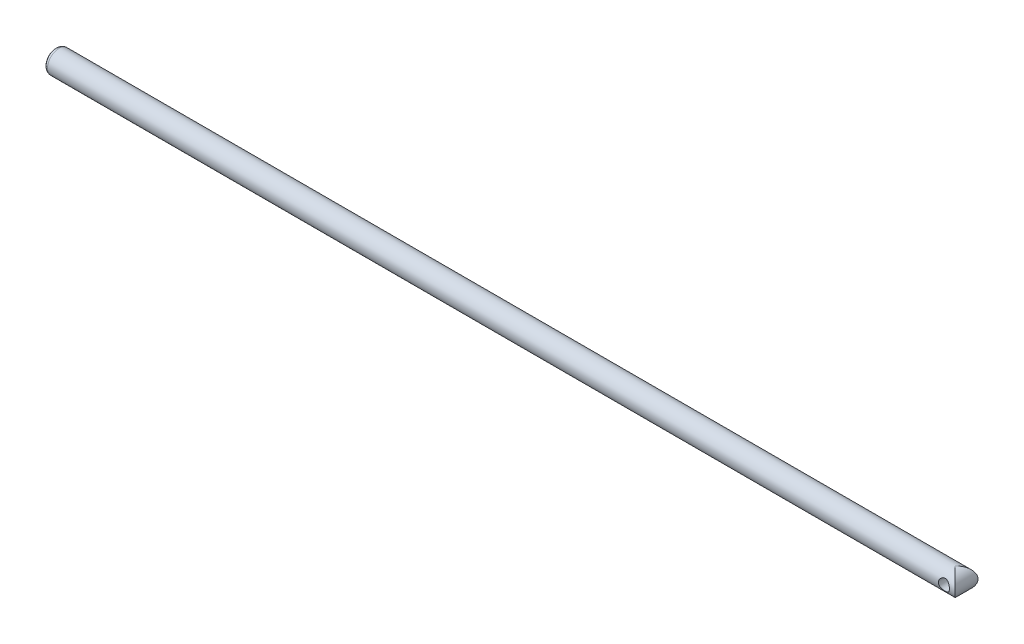
SolidWorks part; units mm, degrees
ref_plane "Front Plane" through (0, 0, 0) normal (0, 0, 1) x (1, 0, 0)
ref_plane "Top Plane" through (0, 0, 0) normal (0, 1, 0) x (1, 0, 0)
ref_plane "Right Plane" through (0, 0, 0) normal (1, 0, 0) x (0, 0, -1)
sketch "Sketch1" plane through (0, 0, 0) normal (1, 0, 0) x (0, 0, -1)
  circle A0 centre (0, 0) radius 2.25
  dimension "D1" = 4.5
extrude "Boss-Extrude1" add sketch "Sketch1" along normal blind 180
fillet "Fillet1" radius 0.75 1 edges at (0, 0, -2.25)
sketch "Sketch2" plane through (0, 0, 0) normal (0, 0, 1) x (1, 0, 0)
  line L0 (180, 2.25) -> (0.75, 2.25) construction
  line L1 (175.5, 2.25) -> (180, 2.25)
  line L2 (175.5, 2.25) -> (175.5, -2.25)
  line L3 (175.5, -2.25) -> (180, -2.25)
  line L4 (180, 2.25) -> (180, -2.25)
  arc A0 (177.75, 2.25) -> (177.75, -2.25) centre (177.75, 0) cw
  circle A1 centre (177.75, 0) radius 1.1
  dimension "D2" = 2.2
  dimension "D1" = 4.5
extrude "Cut-Extrude1" cut sketch "Sketch2" against normal through all both and the other way through all contours L1 A0 L4 | L4 A0 L3 | A1
